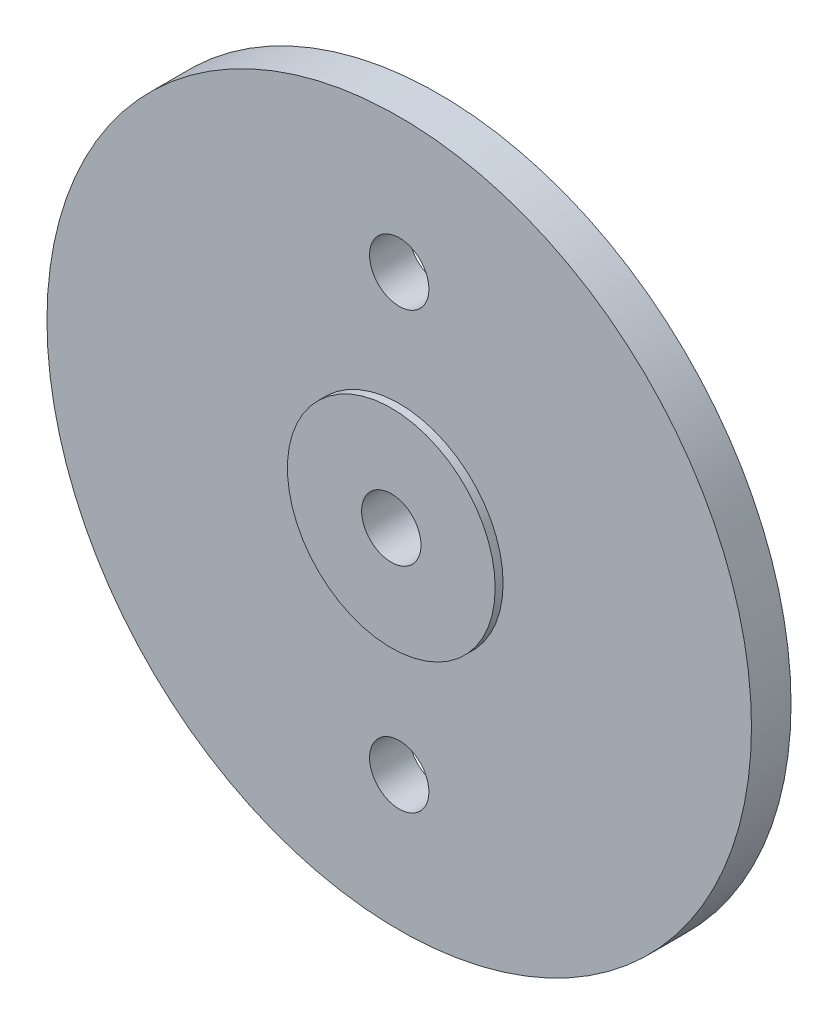
SolidWorks part; units mm, degrees
ref_plane "正面" through (0, 0, 0) normal (0, 0, 1) x (1, 0, 0)
ref_plane "平面" through (0, 0, 0) normal (0, 1, 0) x (1, 0, 0)
ref_plane "右側面" through (0, 0, 0) normal (1, 0, 0) x (0, 0, -1)
sketch "ｽｹｯﾁ1" plane through (0, 0, 0) normal (0, 0, 1) x (1, 0, 0)
  circle A0 centre (0, 0) radius 17.8
extrude "ﾎﾞｽ - 押し出し1" add sketch "ｽｹｯﾁ1" along normal blind 2
sketch "ｽｹｯﾁ2" plane through (0, 0, 0) normal (0, 0, -1) x (-1, 0, 0)
  circle A0 centre (0, 0) radius 7.85
extrude "ﾎﾞｽ - 押し出し2" add sketch "ｽｹｯﾁ2" along normal blind 0.8
draft "抜き勾配1" type of draft neutral plane draft angle 1 faces to draft 1 face at (-7.85, 0, -0.8) neutral plane through (0, 0, -0.8) neutral plane normal (0, 0, -1) parameters "D1"=1
sketch "ｽｹｯﾁ38" plane through (0, 0, -0.8) normal (0, 0, -1) x (-1, 0, 0)
  circle A0 centre (0, 0) radius 4.8
extrude "ﾎﾞｽ - 押し出し3" add sketch "ｽｹｯﾁ38" along normal blind 1.9
sketch "ｽｹｯﾁ39" plane through (0, 0, 2) normal (0, 0, 1) x (1, 0, 0)
  circle A0 centre (0, 0) radius 5.25
extrude "ﾎﾞｽ - 押し出し4" add sketch "ｽｹｯﾁ39" along normal blind 0.4
sketch "ｽｹｯﾁ40" plane through (0, 0, 2.4) normal (0, 0, 1) x (1, 0, 0)
  circle A0 centre (0, 0) radius 1.5
extrude "ｶｯﾄ - 押し出し1" cut sketch "ｽｹｯﾁ40" against normal blind 10.4
sketch "ｽｹｯﾁ42" plane through (0, 0, 2) normal (0, 0, 1) x (1, 0, 0)
  circle A0 centre (0, 11) radius 1.5
  circle A1 centre (0, 0) radius 5.25 construction
  circle A2 centre (0, -11) radius 1.5
  dimension "D1" = 11
  dimension "D2" = 11
extrude "ｶｯﾄ - 押し出し3" cut sketch "ｽｹｯﾁ42" against normal blind 10
